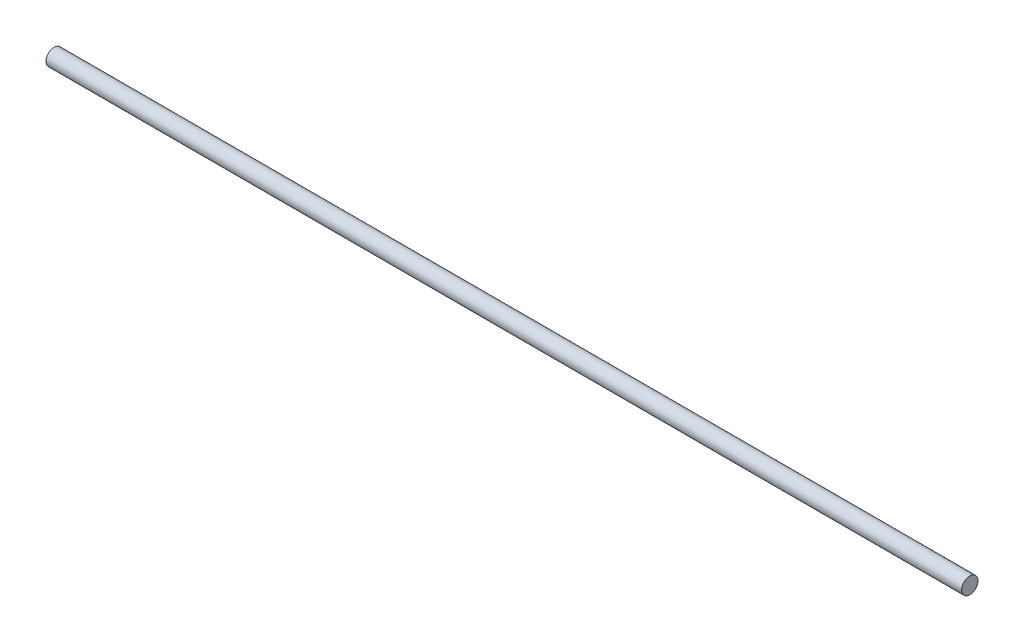
SolidWorks part; units mm, degrees
ref_plane "Front Plane" through (0, 0, 0) normal (0, 0, 1) x (1, 0, 0)
ref_plane "Top Plane" through (0, 0, 0) normal (0, 1, 0) x (1, 0, 0)
ref_plane "Right Plane" through (0, 0, 0) normal (1, 0, 0) x (0, 0, -1)
sketch "Sketch1" plane through (0, 0, 0) normal (1, 0, 0) x (0, 0, -1)
  circle A0 centre (0, 0) radius 2.5
  dimension "D1" = 5
extrude "Boss-Extrude1" add sketch "Sketch1" along normal blind 280
